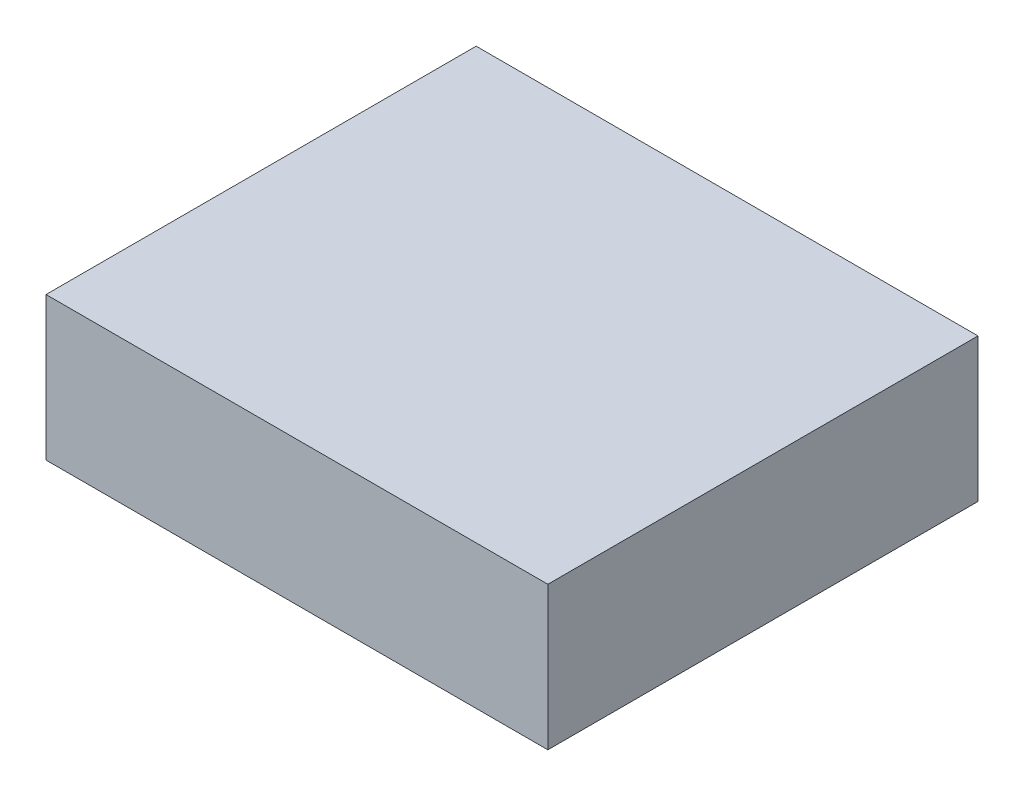
SolidWorks part; units mm, degrees
material "Rubber"
ref_plane "Front Plane" through (0, 0, 0) normal (0, 0, 1) x (1, 0, 0)
ref_plane "Top Plane" through (0, 0, 0) normal (0, 1, 0) x (1, 0, 0)
ref_plane "Right Plane" through (0, 0, 0) normal (1, 0, 0) x (0, 0, -1)
sketch "Sketch1" plane through (0, 0, 0) normal (0, 1, 0) x (1, 0, 0)
  line L1 (-177.8, 152.4) -> (177.8, 152.4)
  line L2 (-177.8, 152.4) -> (-177.8, -152.4)
  line L3 (-177.8, -152.4) -> (177.8, -152.4)
  line L4 (177.8, 152.4) -> (177.8, -152.4)
  line L5 (-177.8, 152.4) -> (177.8, -152.4) construction
  line L6 (-177.8, -152.4) -> (177.8, 152.4) construction
  point P0 (0, 0)
  dimension "D1" = 355.6
  dimension "D2" = 304.8
extrude "Boss-Extrude1" add sketch "Sketch1" along normal blind 101.6
